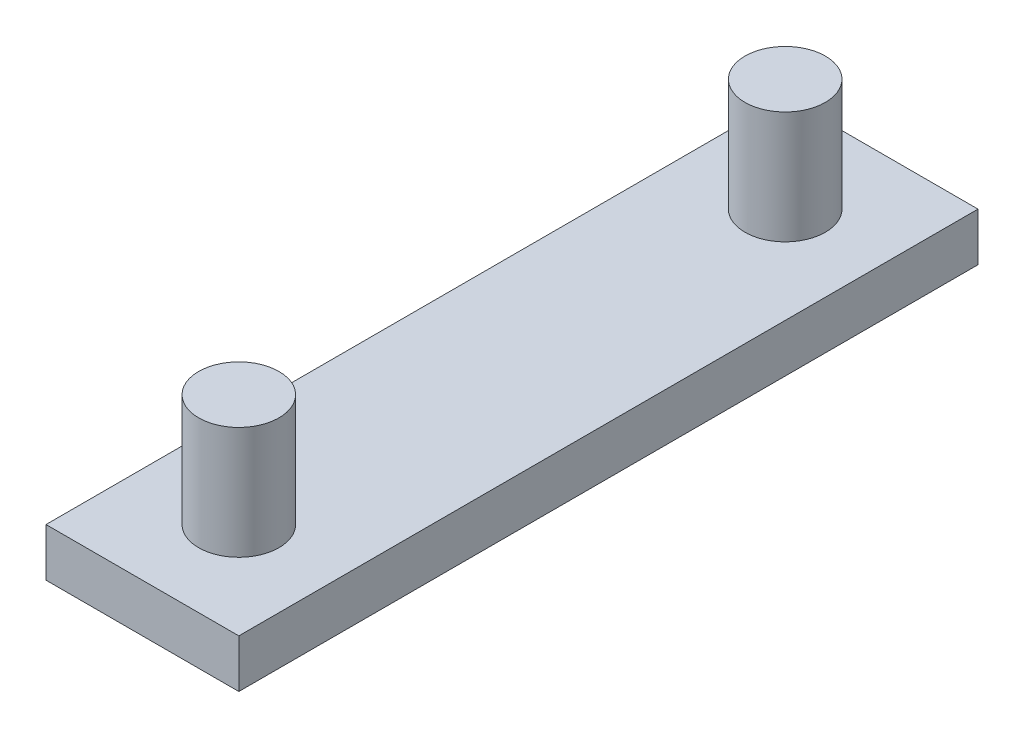
SolidWorks part; units mm, degrees
ref_plane "Front Plane" through (0, 0, 0) normal (0, 0, 1) x (1, 0, 0)
ref_plane "Top Plane" through (0, 0, 0) normal (0, 1, 0) x (1, 0, 0)
ref_plane "Right Plane" through (0, 0, 0) normal (1, 0, 0) x (0, 0, -1)
sketch "Sketch2" plane through (0, 0, 0) normal (0, 1, 0) x (1, 0, 0)
  line L1 (-6.1699, -22.8567) -> (5.8301, -22.8567)
  line L2 (-6.1699, -22.8567) -> (-6.1699, 23.1433)
  line L3 (-6.1699, 23.1433) -> (5.8301, 23.1433)
  line L4 (5.8301, -22.8567) -> (5.8301, 23.1433)
  dimension "D1" = 46
  dimension "D2" = 12
sketch "Sketch3" plane through (0, 0, 0) normal (0, 1, 0) x (1, 0, 0)
  line L2 (5.8301, -22.8567) -> (5.8301, 23.1433) construction
  line L4 (-6.1699, 23.1433) -> (5.8301, 23.1433) construction
  line L5 (5.8301, 0.1433) -> (-6.1699, 0.1433) construction
  line L6 (-6.1699, -22.8567) -> (-6.1699, 23.1433) construction
  circle A2 centre (-0.1699, 17.1433) radius 2.5
  circle A3 centre (-0.1699, -16.8567) radius 2.5
  dimension "D3" = 5
  dimension "D1" = 6
  dimension "D2" = 6
  dimension "D4" = 23
extrude "Boss-Extrude4" add sketch "Sketch3" along normal blind 10
extrude "Boss-Extrude5" add sketch "Sketch2" along normal blind 3
